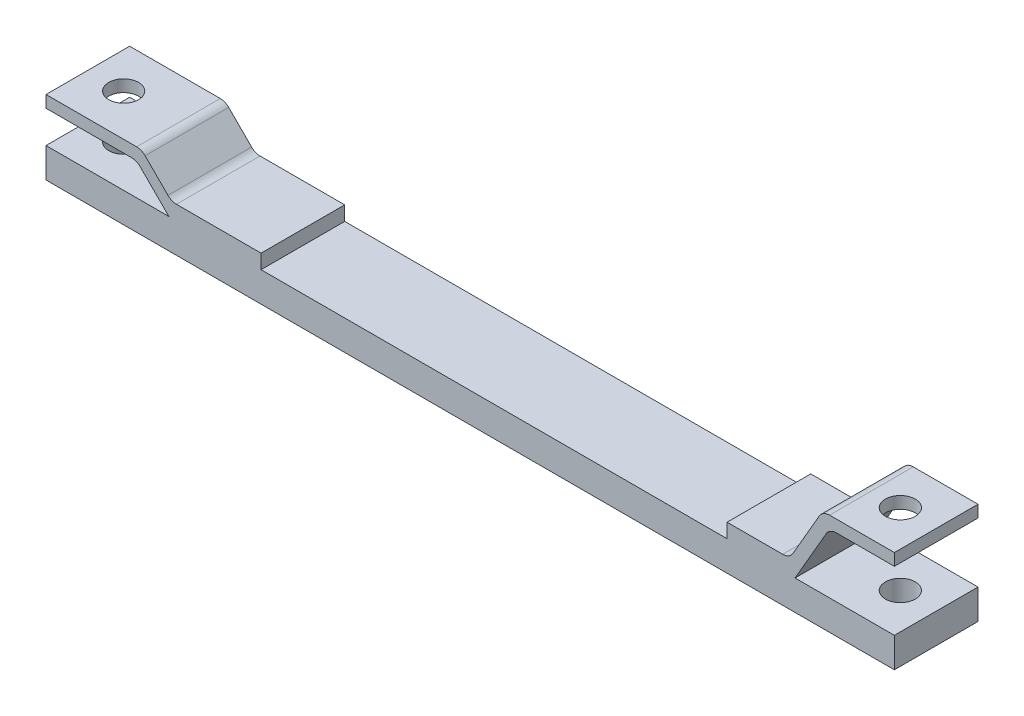
SolidWorks part; units mm, degrees
ref_plane "Front Plane" through (0, 0, 0) normal (0, 0, 1) x (1, 0, 0)
ref_plane "Top Plane" through (0, 0, 0) normal (0, 1, 0) x (1, 0, 0)
ref_plane "Right Plane" through (0, 0, 0) normal (1, 0, 0) x (0, 0, -1)
sketch "Sketch1" plane through (0, 0, 0) normal (0, 0, 1) x (1, 0, 0)
  line L0 (0, 52) -> (75.8579, 52)
  line L1 (0, 0) -> (710, 0)
  line L2 (0, 0) -> (0, 25)
  line L3 (0, 25) -> (710, 25)
  line L4 (710, 0) -> (710, 25)
  line L5 (0, 62) -> (80, 62)
  line L6 (80, 62) -> (105, 37)
  line L7 (105, 37) -> (180, 37)
  line L8 (180, 37) -> (180, 25)
  line L9 (180, 25) -> (710, 25)
  line L10 (75.8579, 52) -> (100.8579, 27)
  line L11 (710, 85) -> (650, 85)
  line L12 (650, 85) -> (622.2872, 37)
  line L13 (622.2872, 37) -> (570, 37)
  line L14 (570, 37) -> (570, 25)
  line L15 (0, 62) -> (0, 52)
  line L16 (100.8579, 27) -> (102.8579, 25)
  line L17 (710, 85) -> (710, 75)
  line L18 (710, 75) -> (655.7735, 75)
  line L19 (655.7735, 75) -> (628.0607, 27)
  line L20 (628.0607, 27) -> (626.906, 25)
  line L22 (628.0607, 27) -> (580, 27) construction
  line L23 (170, 15) -> (710, 15) construction
  line L24 (580, 27) -> (580, 25) construction
  line L25 (100.8579, 27) -> (170, 27) construction
  line L26 (170, 27) -> (170, 15) construction
  dimension "D1" = 710
  dimension "D2" = 25
  dimension "D3" = 80
  dimension "D4" = 12
  dimension "D5" = 37
  dimension "D6" = 180
  dimension "D7" = 45
  dimension "D8" = 60
  dimension "D9" = 60
  dimension "D10" = 60
  dimension "D11" = 12
  dimension "D12" = 140
  dimension "D13" = 10
  dimension "D14" = 10
extrude "Boss-Extrude1" add sketch "Sketch1" along normal blind 70 contours L10 L16 L3 L8 L7 L6 L5 L15 L0 | L20 L19 L18 L17 L11 L12 L13 L14 L9
fillet "Fillet1" radius 10 4 edges at (622.2872, 37, 35) (650, 85, 35) (105, 37, 35) (80, 62, 35)
fillet "Fillet2" radius 10 2 edges at (655.7735, 75, 35) (75.8579, 52, 35)
sketch "Sketch2" plane through (0, 85, 0) normal (0, 1, 0) x (1, 0, 0)
  line L0 (710, -70) -> (710, 0) construction
  line L1 (0, -70) -> (0, 0) construction
  circle A0 centre (680, -35) radius 12.5
  circle A1 centre (30, -35) radius 12.5
  point P8 (710, -35)
  dimension "D1" = 25
  dimension "D2" = 25
  dimension "D3" = 30
  dimension "D4" = 30
extrude "Cut-Extrude1" cut sketch "Sketch2" against normal through all
